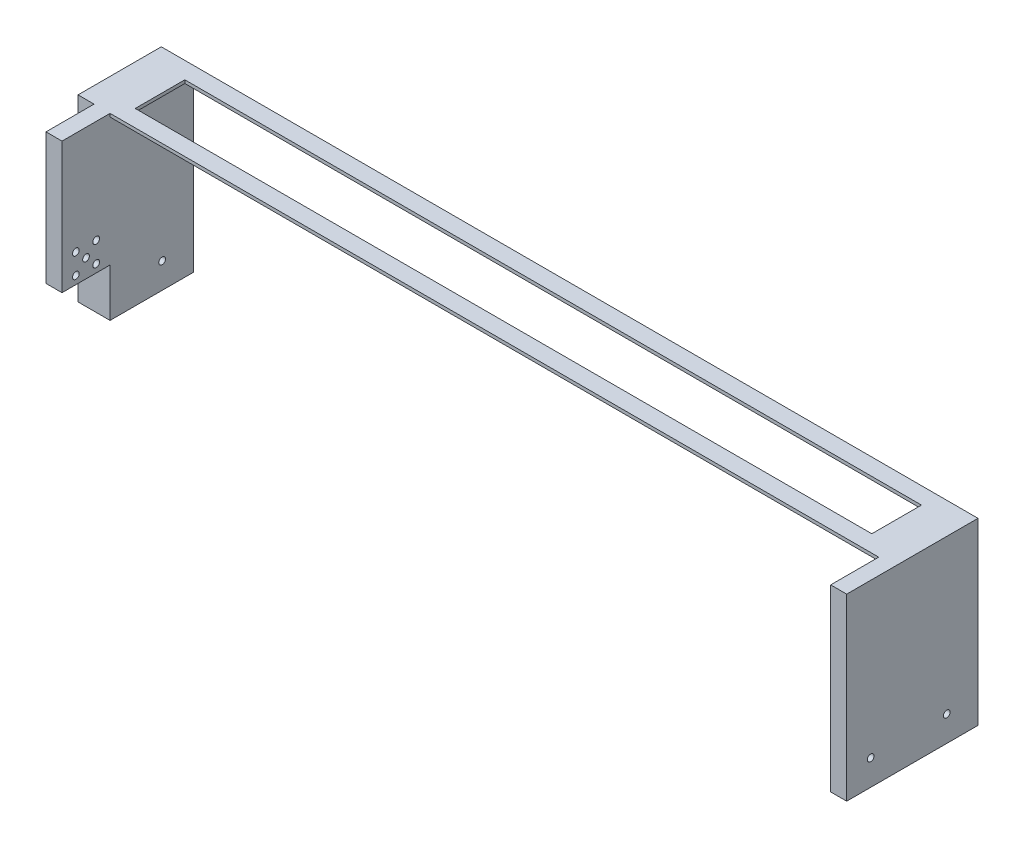
SolidWorks part; units mm, degrees
ref_plane "Front Plane" through (0, 0, 0) normal (0, 0, 1) x (1, 0, 0)
ref_plane "Top Plane" through (0, 0, 0) normal (0, 1, 0) x (1, 0, 0)
ref_plane "Right Plane" through (0, 0, 0) normal (1, 0, 0) x (0, 0, -1)
sketch "Sketch1" plane through (0, 0, 0) normal (0, 1, 0) x (1, 0, 0)
  line L0 (10, -82) -> (10, -52)
  line L1 (10, -52) -> (0, -52)
  line L2 (0, -52) -> (0, 0)
  line L4 (0, 0) -> (510, 0)
  line L5 (510, 0) -> (510, -82)
  line L8 (510, -82) -> (500, -82)
  line L9 (20, -82) -> (20, -52)
  line L10 (20, -52) -> (500, -52)
  line L11 (500, -52) -> (500, -82)
  line L12 (20, -82) -> (10, -82)
  dimension "D1" = 480
  dimension "D2" = 510
  dimension "D3" = 10
  dimension "D4" = 10
  dimension "D5" = 52
  dimension "D6" = 30
  dimension "D7" = 30
extrude "Boss-Extrude1" add sketch "Sketch1" along normal blind 82 and the other way blind 0.001 contours L9 L10 L11 L8 L5 L4 L2 L1 L0 L12
sketch "Sketch2" plane through (0, 0, 0) normal (0, 0, 1) x (1, 0, 0)
  line L0 (20, -0.001) -> (20, 79.999)
  line L1 (20, 82) -> (20, -0.001) construction
  line L2 (20, 79.999) -> (500, 79.999)
  line L3 (500, 82) -> (500, -0.001) construction
  line L4 (500, 79.999) -> (500, -0.001)
  line L5 (500, -0.001) -> (20, -0.001)
  dimension "D1" = 80
extrude "Cut-Extrude2" cut sketch "Sketch2" along normal blind 82
sketch "Sketch3" plane through (0, 0, 0) normal (0, 1, 0) x (1, 0, 0)
  line L0 (20, -82) -> (20, -52) construction
  line L1 (0, 0) -> (20, 0)
  line L2 (0, 0) -> (0, -52)
  line L3 (0, -52) -> (20, -52)
  line L4 (20, 0) -> (20, -52)
  line L5 (0, 0) -> (510, 0) construction
  line L6 (500, 0) -> (510, 0)
  line L7 (500, 0) -> (500, -82)
  line L8 (500, -82) -> (510, -82)
  line L9 (510, 0) -> (510, -82)
  line L10 (500, -52) -> (500, -82) construction
  line L11 (10, -52) -> (0, -52) construction
extrude "Boss-Extrude3" add sketch "Sketch3" against normal blind 30
sketch "Sketch4" plane through (510, 0, 0) normal (1, 0, 0) x (0, 0, -1)
  line L0 (-82, -30) -> (0, -30) construction
  line L2 (-82, -30) -> (-82, 82) construction
  circle A0 centre (-67, -14.051) radius 2.1
  circle A1 centre (-19.5, -14.05) radius 2.1
  dimension "D1" = 4.2
  dimension "D2" = 4.2
  dimension "D3" = 15.949
  dimension "D4" = 15
  dimension "D5" = 15.95
  dimension "D6" = 47.5
extrude "Cut-Extrude3" cut sketch "Sketch4" against normal blind 618
sketch "Sketch5" plane through (0, 82, 0) normal (0, 1, 0) x (1, 0, 0)
  line L0 (25.2, 0) -> (25.2, -52) construction
  line L1 (0, 0) -> (510, 0) construction
  line L2 (20, -82) -> (20, -52) construction
  line L3 (20, -52) -> (500, -52) construction
  line L4 (485.2, 0) -> (485.2, -52) construction
  line L5 (25.2, -594.2105) -> (25.2, 455.7895) construction
  line L6 (25.2, -10.5) -> (485.2, -10.5)
  line L7 (25.2, -10.5) -> (25.2, -41.5)
  line L8 (25.2, -41.5) -> (485.2, -41.5)
  line L9 (485.2, -41.5) -> (485.2, -10.5)
  dimension "D1" = 10.5
  dimension "D2" = 31
extrude "Cut-Extrude4" cut sketch "Sketch5" against normal blind 42
sketch "Sketch6" plane through (20, 0, 0) normal (1, 0, 0) x (0, 0, -1)
  line L0 (-82, -0.001) -> (-52, -0.001) construction
  line L3 (-67, -0.001) -> (-67, 29.5711) construction
  circle A0 centre (-67, 11.349) radius 2.1
  circle A1 centre (-60.65, 17.699) radius 2.1
  circle A2 centre (-73.35, 17.699) radius 2.1
  circle A3 centre (-73.35, 4.999) radius 2.1
  circle A4 centre (-60.65, 4.999) radius 2.1
  dimension "D5" = 4.2
  dimension "D6" = 12.7
  dimension "D1" = 12.7
  dimension "D2" = 6.35
  dimension "D3" = 12.7
  dimension "D4" = 6.35
  dimension "D7" = 6.35
  dimension "D8" = 6.35
  dimension "D9" = 6.35
  dimension "D10" = 5
  dimension "D11" = 29.5721
extrude "Cut-Extrude5" cut sketch "Sketch6" against normal blind 10
